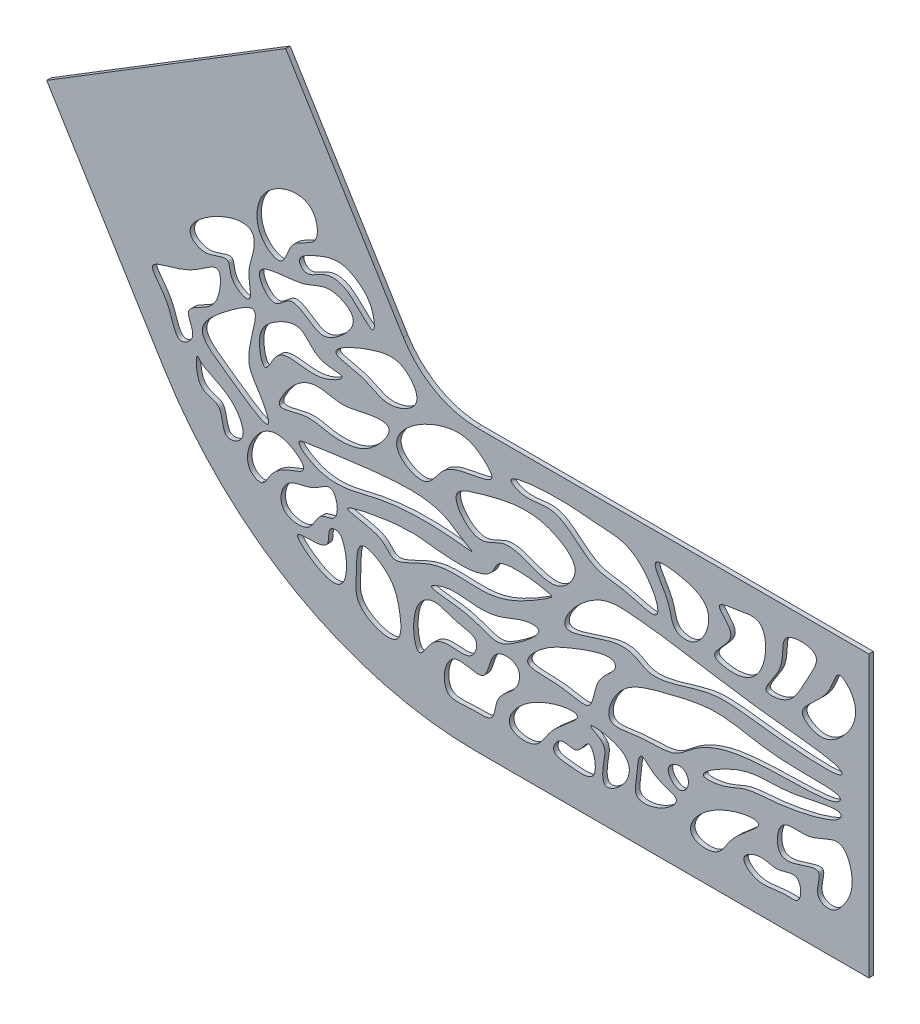
SolidWorks part; units mm, degrees
ref_plane "Alzado" through (0, 0, 0) normal (0, 0, 1) x (1, 0, 0)
ref_plane "Planta" through (0, 0, 0) normal (0, 1, 0) x (1, 0, 0)
ref_plane "Vista lateral" through (0, 0, 0) normal (1, 0, 0) x (0, 0, -1)
sketch "Croquis1" plane through (0, 0, 0) normal (0, 0, 1) x (1, 0, 0)
  line L0 (-108.8464, -21.6986) -> (-38.8648, -21.6986)
  line L1 (-108.7179, 28.3014) -> (-38.8648, 28.3014)
  line L2 (-164.4187, 9.5015) -> (-180.1367, 35.0543)
  line L3 (-121.8307, 35.6981) -> (-137.5487, 61.2509)
  line L8 (-38.8648, 28.3014) -> (-38.8648, -21.6986)
  line L9 (-185.376, 43.5719) -> (-142.7881, 69.7685)
  line L10 (-137.5487, 61.2509) -> (-142.7881, 69.7685)
  line L11 (-180.1367, 35.0543) -> (-185.376, 43.5719)
  arc A0 (-164.4187, 9.5015) -> (-108.8464, -21.6986) centre (-108.5959, 43.8391) ccw
  arc A1 (-121.8307, 35.6981) -> (-108.7179, 28.3014) centre (-108.5959, 43.8391) ccw
  spline S0 degree 3 poles (-100.4055, 3.1812) (-96.2096, 2.6407) (-101.6833, -1.5799) (-105.0602, -3.3903) (-109.3149, -1.5246) (-112.0327, -1.0245) (-118.0527, -0.4678) (-113.717, 1.2519) (-110.3815, 0.7431) (-104.7095, 0.4434) (-100.4055, 3.1812) (-96.2096, 2.6407) (-101.6833, -1.5799) knots -0.315598 -0.18303 -0.018303 0 0.157145 0.229142 0.313252 0.454214 0.526143 0.577742 0.684402 0.81697 0.981697 1 1.157145 1.229142 1.313252 only from (-97.9879, 2.8318) to (-97.9879, 2.8318)
  spline S1 degree 3 poles (-95.9708, 8.2792) (-94.8978, 9.2475) (-104.9487, 10.9619) (-106.2863, 4.0053) (-119.0084, 6.6049) (-121.4988, 6.1089) (-121.9242, 6.6756) (-135.6785, 4.0526) (-124.9898, 3.3533) (-123.9896, -0.7488) (-114.1156, 5.6842) (-106.5443, 1.3252) (-95.9708, 8.2792) (-94.8978, 9.2475) (-104.9487, 10.9619) knots -0.283645 -0.122304 -0.01223 0 0.069569 0.096182 0.247246 0.281231 0.417147 0.513763 0.586005 0.643687 0.716355 0.877696 0.98777 1 1.069569 1.096182 1.247246 only from (-95.3982, 8.9779) to (-95.3982, 8.9779)
  spline S2 degree 3 poles (-107.3413, 7.7106) (-113.3834, 10.7699) (-114.9259, 14.2602) (-133.5623, 11.5959) (-141.7052, 10.4053) (-135.231, 5.8797) (-119.8086, 11.3799) (-107.3413, 7.7106) (-113.3834, 10.7699) (-114.9259, 14.2602) knots -0.400334 -0.311414 -0.031141 0 0.352571 0.531394 0.556104 0.599666 0.688586 0.968859 1 1.352571 1.531394 1.556104 only from (-110.4424, 9.293) to (-110.4424, 9.293)
  spline S3 degree 3 poles (-84.2507, 5.5512) (-83.8734, 2.8356) (-88.0597, 0.6541) (-87.7211, -4.9686) (-90.9541, -4.7807) (-94.5619, -3.8245) (-101.6758, -4.5392) (-97.1613, 0.3592) (-92.3688, 2.6509) (-84.2507, 5.5512) (-83.8734, 2.8356) (-88.0597, 0.6541) knots -0.316899 -0.167029 -0.016703 0 0.100038 0.223753 0.272835 0.361932 0.526926 0.683101 0.832971 0.983297 1 1.100038 1.223753 1.272835 only from (-84.0361, 3.6856) to (-84.0361, 3.6856)
  spline S4 degree 3 poles (-43.868, -0.7672) (-43.7102, 2.1599) (-55.24, -1.3998) (-60.0633, 0.7583) (-70.5442, -5.7193) (-64.4294, -5.2693) (-60.8295, -3.0718) (-54.31, -3.2065) (-43.868, -0.7672) (-43.7102, 2.1599) (-55.24, -1.3998) knots -0.352515 -0.233319 -0.023332 0 0.173914 0.388453 0.503873 0.557099 0.647485 0.766681 0.976668 1 1.173914 1.388453 1.503873 only from (-43.8469, 1.0338) to (-43.8469, 1.0338)
  spline S5 degree 3 poles (-45.1762, 1.1703) (-43.1361, 4.4758) (-56.6574, 3.4944) (-65.1405, 6.7295) (-75.3032, 4.0837) (-83.5561, 1.9737) (-86.6828, -6.3448) (-78.8751, -4.5062) (-73.6633, -5.2307) (-69.3516, -0.9035) (-60.2894, 2.5904) (-45.1762, 1.1703) (-43.1361, 4.4758) (-56.6574, 3.4944) knots -0.295039 -0.191816 -0.019182 0 0.11455 0.24602 0.351314 0.440261 0.51992 0.570513 0.65581 0.704961 0.808184 0.980818 1 1.11455 1.24602 1.351314 only from (-43.9298, 3.407) to (-43.9298, 3.407)
  spline S6 degree 3 poles (-42.4061, 6.1723) (-44.7626, 8.8048) (-61.1588, 9.8682) (-75.7985, 13.0975) (-88.9426, 13.5997) (-97.4981, 1.9663) (-81.6724, 9.2245) (-78.2315, 3.8358) (-67.2533, 9.1986) (-59.1086, 7.4821) (-42.4061, 6.1723) (-44.7626, 8.8048) (-61.1588, 9.8682) knots -0.2879 -0.155387 -0.015539 0 0.099677 0.267068 0.297768 0.406678 0.472741 0.561818 0.7121 0.844613 0.984461 1 1.099677 1.267068 1.297768 only from (-44.0875, 7.9226) to (-44.0875, 7.9226)
  spline S7 degree 3 poles (-55.7688, -13.77) (-55.1878, -4.2136) (-49.0734, -6.2918) (-43.5652, -1.4931) (-41.1669, -8.4852) (-42.8129, -12.2637) (-45.3318, -15.0294) (-48.9687, -13.8335) (-45.7299, -6.9917) (-55.7688, -13.77) (-55.1878, -4.2136) (-49.0734, -6.2918) knots -0.371419 -0.276319 -0.113656 0 0.115773 0.264232 0.386481 0.50234 0.57949 0.628581 0.723681 0.886344 1 1.115773 1.264232 1.386481 only from (-54.3633, -5.9471) to (-54.3633, -5.9471)
  spline S8 degree 3 poles (-89.9303, 15.357) (-95.1992, 8.0201) (-102.3681, 15.1916) (-108.6497, 9.5021) (-114.501, 16.4978) (-104.308, 19.5679) (-97.2634, 21.2185) (-89.9303, 15.357) (-95.1992, 8.0201) (-102.3681, 15.1916) knots -0.482978 -0.177957 -0.098974 0 0.209597 0.303826 0.431796 0.517022 0.822043 0.901026 1 1.209597 1.303826 1.431796 only from (-93.8287, 11.2805) to (-93.8287, 11.2805)
  spline S9 degree 3 poles (-92.8384, 25.0424) (-104.6179, 23.9678) (-99.7607, 21.3466) (-94.0994, 23.914) (-88.8244, 16.449) (-82.5807, 16.8034) (-74.1656, 13.4308) (-79.6794, 24.1391) (-87.746, 23.9509) (-92.8384, 25.0424) (-104.6179, 23.9678) (-99.7607, 21.3466) knots -0.391213 -0.273847 -0.12925 0 0.018174 0.122894 0.279654 0.384629 0.472626 0.608787 0.726153 0.87075 1 1.018174 1.122894 1.279654 only from (-102.3447, 22.7981) to (-102.3447, 22.7981)
  spline S10 degree 3 poles (-71.4074, 23.6007) (-79.1145, 24.4495) (-74.0473, 18.8668) (-74.0962, 14.6634) (-69.0518, 13.4732) (-65.6689, 21.0574) (-71.4074, 23.6007) (-79.1145, 24.4495) (-74.0473, 18.8668) knots -0.597987 -0.351672 -0.165698 0 0.195722 0.325152 0.402013 0.648328 0.834302 1 1.195722 1.325152 1.402013 only from (-76.838, 23.4212) to (-76.838, 23.4212)
  spline S11 degree 3 poles (-61.8839, 23.3906) (-67.2302, 22.7481) (-60.7833, 18.6226) (-68.6479, 14.2898) (-61.93, 12.7387) (-56.9891, 15.3549) (-56.8321, 24.5733) (-61.8839, 23.3906) (-67.2302, 22.7481) (-60.7833, 18.6226) knots -0.438785 -0.218352 -0.095301 0 0.113934 0.288077 0.377524 0.561215 0.781648 0.904699 1 1.113934 1.288077 1.377524 only from (-65.5021, 22.4009) to (-65.5021, 22.4009)
  spline S12 degree 3 poles (-46.5328, 24.3689) (-55.4956, 24.5197) (-52.9941, 18.3631) (-58.8247, 13.0598) (-52.3517, 13.3454) (-50.8304, 17.697) (-46.5328, 24.3689) (-55.4956, 24.5197) (-52.9941, 18.3631) knots -0.577089 -0.309658 -0.16535 0 0.184162 0.363281 0.422911 0.690342 0.83465 1 1.184162 1.363281 1.422911 only from (-53.3642, 23.579) to (-53.3642, 23.579)
  spline S13 degree 3 poles (-47.3156, 10.5592) (-53.1941, 13.8063) (-45.7071, 16.9785) (-44.6822, 23.6828) (-39.6806, 18.815) (-42.7244, 13.2199) (-47.3156, 10.5592) (-53.1941, 13.8063) (-45.7071, 16.9785) knots -0.509276 -0.239068 -0.105487 0 0.2678 0.390798 0.490724 0.760932 0.894513 1 1.2678 1.390798 1.490724 only from (-50.5162, 12.7661) to (-50.5162, 12.7661)
  spline S14 degree 3 poles (-114.3123, 27.5218) (-127.7642, 19.0347) (-116.9289, 13.759) (-114.9315, 21.4169) (-103.8286, 20.3023) (-108.4139, 25.0459) (-114.3123, 27.5218) (-127.7642, 19.0347) (-116.9289, 13.759) knots -0.520669 -0.45976 -0.334427 0 0.125653 0.267573 0.479331 0.54024 0.665573 1 1.125653 1.267573 1.479331 only from (-122.6003, 17.4019) to (-122.6003, 17.4019)
  spline S15 degree 3 poles (-124.8384, 22.9479) (-117.5427, 26.4016) (-121.8712, 31.9946) (-127.1678, 31.4577) (-137.2402, 26.9685) (-128.4706, 26.2208) (-124.8384, 22.9479) (-117.5427, 26.4016) (-121.8712, 31.9946) knots -0.472759 -0.332235 -0.177614 0 0.136647 0.282006 0.527241 0.667765 0.822386 1 1.136647 1.282006 1.527241 only from (-119.4126, 27.1855) to (-119.4126, 27.1855)
  spline S16 degree 3 poles (-129.234, 20.564) (-122.3531, 21.6843) (-126.9414, 15.708) (-130.5959, 14.1258) (-135.2719, 14.0042) (-138.8407, 15.5363) (-145.1218, 12.9324) (-141.8386, 18.6302) (-138.0302, 21.2681) (-132.91, 19.5279) (-129.234, 20.564) (-122.3531, 21.6843) (-126.9414, 15.708) knots -0.286611 -0.187119 -0.108143 0 0.112894 0.20603 0.295443 0.40419 0.500293 0.567623 0.713389 0.812881 0.891857 1 1.112894 1.20603 1.295443 only from (-124.4482, 20.4625) to (-124.4482, 20.4625)
  spline S17 degree 3 poles (-137.6702, 24.1356) (-130.8633, 24.7204) (-138.5446, 20.2847) (-143.6646, 24.5688) (-146.6063, 17.0402) (-148.2178, 23.6202) (-145.2568, 26.6521) (-139.5982, 29.0688) (-137.6702, 24.1356) (-130.8633, 24.7204) (-138.5446, 20.2847) knots -0.352083 -0.229209 -0.097257 0 0.098282 0.334563 0.412197 0.510953 0.647917 0.770791 0.902743 1 1.098282 1.334563 1.412197 only from (-132.7506, 24.1353) to (-132.7506, 24.1353)
  spline S18 degree 3 poles (-132.9555, 30.0213) (-137.3951, 27.7667) (-141.3938, 33.2812) (-144.8297, 28.0526) (-150.2386, 35.0566) (-139.6852, 33.9035) (-135.4498, 37.4594) (-128.8707, 34.3929) (-132.9555, 30.0213) (-137.3951, 27.7667) (-141.3938, 33.2812) knots -0.322381 -0.205976 -0.070065 0 0.160698 0.23687 0.338533 0.549422 0.677619 0.794024 0.929935 1 1.160698 1.23687 1.338533 only from (-136.3173, 28.837) to (-136.3173, 28.837)
  spline S19 degree 3 poles (-127.2551, 37.7466) (-126.517, 31.9582) (-131.4569, 38.7164) (-135.8465, 38.9472) (-139.0186, 36.3001) (-141.0989, 38.7954) (-136.523, 41.0093) (-133.0068, 42.0964) (-129.2255, 39.9202) (-127.2551, 37.7466) (-126.517, 31.9582) (-131.4569, 38.7164) knots -0.283469 -0.193959 -0.083465 0 0.17174 0.311461 0.414653 0.444427 0.554647 0.716531 0.806041 0.916535 1 1.17174 1.311461 1.414653 only from (-127.0917, 34.2547) to (-127.0917, 34.2547)
  spline S20 degree 3 poles (-153.9745, 23.6251) (-145.9826, 29.1645) (-150.7946, 18.5836) (-147.5723, 14.7564) (-144.0136, 7.6492) (-153.0248, 14.321) (-159.7256, 18.7033) (-153.9745, 23.6251) (-145.9826, 29.1645) (-150.7946, 18.5836) knots -0.426096 -0.279271 -0.118317 0 0.192488 0.293022 0.387178 0.573904 0.720729 0.881683 1 1.192488 1.293022 1.387178 only from (-148.529, 26.6062) to (-148.529, 26.6062)
  spline S21 degree 3 poles (-55.2274, -13.7251) (-50.8574, -11.1441) (-50.705, -16.5564) (-55.1905, -15.9395) (-58.4243, -17.6543) (-62.1609, -14.0138) (-57.9612, -12.0342) (-55.2274, -13.7251) (-50.8574, -11.1441) (-50.705, -16.5564) knots -0.419869 -0.272796 -0.144259 0 0.160267 0.210766 0.504987 0.580131 0.727204 0.855741 1 1.160267 1.210766 1.504987 only from (-51.6792, -12.6886) to (-51.6792, -12.6886)
  spline S22 degree 3 poles (-67.6542, -8.2805) (-72.4924, -16.003) (-65.6748, -16.6786) (-63.614, -12.4117) (-61.017, -10.3992) (-56.3303, -6.3587) (-67.6542, -8.2805) (-72.4924, -16.003) (-65.6748, -16.6786) knots -0.566614 -0.504093 -0.218818 0 0.131217 0.261968 0.433386 0.495907 0.781182 1 1.131217 1.261968 1.433386 only from (-70.1781, -15.5973) to (-70.1781, -15.5973)
  spline S23 degree 3 poles (-99.9275, -7.7956) (-104.7656, -15.5181) (-97.948, -16.1937) (-95.8873, -11.9268) (-93.2903, -9.9144) (-88.6036, -5.8738) (-99.9275, -7.7956) (-104.7656, -15.5181) (-97.948, -16.1937) knots -0.566614 -0.504093 -0.218818 0 0.131217 0.261968 0.433386 0.495907 0.781182 1 1.131217 1.261968 1.433386 only from (-102.4513, -15.1124) to (-102.4513, -15.1124)
  spline S24 degree 3 poles (-90.7044, -13.7114) (-93.8141, -11.5745) (-95.8994, -15.2616) (-91.4989, -15.6406) (-86.509, -16.3126) (-88.4979, -8.5136) (-90.7044, -13.7114) (-93.8141, -11.5745) (-95.8994, -15.2616) knots -0.50021 -0.292274 -0.145876 0 0.117021 0.265473 0.49979 0.707726 0.854124 1 1.117021 1.265473 1.49979 only from (-93.8287, -12.572) to (-93.8287, -12.572)
  spline S25 degree 3 poles (-80.1594, -7.8225) (-90.9119, -6.8547) (-85.3096, -9.1276) (-86.3096, -12.1094) (-86.4236, -16.5083) (-81.8895, -13.8633) (-80.1594, -7.8225) (-90.9119, -6.8547) (-85.3096, -9.1276) knots -0.618588 -0.487424 -0.262237 0 0.100832 0.255151 0.381412 0.512576 0.737763 1 1.100832 1.255151 1.381412 only from (-88.3491, -7.7329) to (-88.3491, -7.7329)
  spline S26 degree 3 poles (-76.8185, -10.324) (-79.9765, -6.2217) (-80.118, -11.2204) (-80.9688, -15.0683) (-76.0501, -14.727) (-71.4055, -10.7123) (-76.8185, -10.324) (-79.9765, -6.2217) (-80.118, -11.2204) knots -0.521013 -0.326779 -0.141819 0 0.174988 0.298356 0.478987 0.673221 0.858181 1 1.174988 1.298356 1.478987 only from (-79.3886, -7.7329) to (-79.3886, -7.7329)
  spline S27 degree 3 poles (-71.9311, -5.131) (-75.9801, -6.9854) (-72.5698, -10.6148) (-70.519, -7.8251) (-71.9311, -5.131) (-75.9801, -6.9854) (-72.5698, -10.6148) knots -0.695992 -0.473766 -0.274772 0 0.304008 0.526234 0.725228 1 1.304008 1.526234 1.725228 only from (-74.5935, -7.1958) to (-74.5935, -7.1958)
  spline S28 degree 3 poles (-106.285, -11.5733) (-106.7296, -3.8104) (-100.7975, -4.3413) (-101.2848, -9.2207) (-105.5464, -10.5774) (-105.4198, -15.987) (-109.9024, -15.2962) (-115.4243, -16.6274) (-114.069, -7.0875) (-106.285, -11.5733) (-106.7296, -3.8104) (-100.7975, -4.3413) knots -0.414748 -0.267488 -0.136298 0 0.09281 0.157708 0.299308 0.383949 0.472166 0.585252 0.732512 0.863702 1 1.09281 1.157708 1.299308 only from (-105.0472, -4.7669) to (-105.0472, -4.7669)
  spline S29 degree 3 poles (-116.9345, -8.5594) (-113.6599, -7.2332) (-109.5453, -8.6127) (-108.1136, -3.9651) (-112.7948, -3.6815) (-116.3432, -1.4714) (-120.8072, -4.9288) (-119.6091, -14.1111) (-116.9345, -8.5594) (-113.6599, -7.2332) (-109.5453, -8.6127) knots -0.408616 -0.196902 -0.09815 0 0.139916 0.219187 0.321205 0.480174 0.591384 0.803098 0.90185 1 1.139916 1.219187 1.321205 only from (-113.9347, -7.7329) to (-113.9347, -7.7329)
  spline S30 degree 3 poles (-122.4605, -6.214) (-121.5633, -13.7191) (-130.8452, -10.3851) (-130.0541, -5.114) (-130.3042, 1.6926) (-123.8184, -2.145) (-122.4605, -6.214) (-121.5633, -13.7191) (-130.8452, -10.3851) knots -0.475837 -0.304992 -0.16379 0 0.222453 0.374091 0.524163 0.695008 0.83621 1 1.222453 1.374091 1.524163 only from (-122.9798, -11.4655) to (-122.9798, -11.4655)
  spline S31 degree 3 poles (-131.7069, -2.936) (-131.6896, -10.0276) (-137.6584, -7.5507) (-142.7034, -2.8826) (-134.0857, -4.9334) (-135.6088, 0.0238) (-133.1514, 0.0311) (-131.7069, -2.936) (-131.6896, -10.0276) (-137.6584, -7.5507) knots -0.311497 -0.248093 -0.216943 0 0.243329 0.360779 0.579241 0.688503 0.751907 0.783057 1 1.243329 1.360779 1.579241 only from (-132.7506, -7.7329) to (-132.7506, -7.7329)
  spline S32 degree 3 poles (-142.8882, 4.1867) (-144.535, -2.3549) (-138.0095, -3.2082) (-137.1992, 1.2642) (-132.8436, 1.0923) (-134.0498, 7.5814) (-138.2705, 3.4266) (-142.8882, 4.1867) (-144.535, -2.3549) (-138.0095, -3.2082) knots -0.457136 -0.34329 -0.145044 0 0.167631 0.302485 0.389236 0.542864 0.65671 0.854956 1 1.167631 1.302485 1.389236 only from (-143.2643, -1.3326) to (-143.2643, -1.3326)
  spline S33 degree 3 poles (-148.1282, 9.3257) (-151.0578, 1.7635) (-146.7703, 0.2461) (-145.7179, 2.5054) (-144.0449, 4.237) (-141.8667, 5.1964) (-138.308, 6.3528) (-142.7795, 9.9641) (-148.1282, 9.3257) (-151.0578, 1.7635) (-146.7703, 0.2461) knots -0.593653 -0.458057 -0.281382 0 0.055986 0.125037 0.23029 0.322646 0.406347 0.541943 0.718618 1 1.055986 1.125037 1.23029 only from (-148.529, 1.024) to (-148.529, 1.024)
  spline S34 degree 3 poles (-158.8318, 15.0335) (-157.2516, 12.7956) (-152.2932, 12.1284) (-149.1561, 5.5262) (-154.3564, 3.7675) (-153.6251, 10.0131) (-158.8351, 8.6361) (-158.8318, 15.0335) (-157.2516, 12.7956) (-152.2932, 12.1284) knots -0.28822 -0.12709 -0.012709 0 0.265528 0.46936 0.552103 0.71178 0.87291 0.987291 1 1.265528 1.46936 1.552103 only from (-158.2655, 14.2392) to (-158.2655, 14.2392)
  spline S35 degree 3 poles (-163.081, 20.3877) (-162.4809, 13.8898) (-158.3009, 17.2455) (-161.5248, 21.0043) (-156.4878, 22.5782) (-154.4529, 25.3661) (-154.1097, 31.6548) (-160.058, 25.6322) (-169.0534, 25.3791) (-163.081, 20.3877) (-162.4809, 13.8898) (-158.3009, 17.2455) knots -0.439567 -0.253616 -0.130815 0 0.058503 0.146138 0.242132 0.335973 0.426326 0.560433 0.746384 0.869185 1 1.058503 1.146138 1.242132 only from (-161.1514, 15.3614) to (-161.1514, 15.3614)
  spline S36 degree 3 poles (-152.597, 33.1957) (-152.9183, 28.899) (-148.2503, 26.5347) (-149.925, 32.1094) (-148.514, 34.6827) (-148.1075, 40.2844) (-155.9709, 38.2071) (-161.4268, 32.8978) (-156.6902, 30.3134) (-152.597, 33.1957) (-152.9183, 28.899) (-148.2503, 26.5347) knots -0.254814 -0.174445 -0.066097 0 0.09497 0.186427 0.312723 0.374421 0.581872 0.745186 0.825555 0.933903 1 1.09497 1.186427 1.312723 only from (-152.3501, 29.5381) to (-152.3501, 29.5381)
  spline S37 degree 3 poles (-148.6859, 47.176) (-148.3959, 38.1421) (-142.8842, 35.6775) (-142.2892, 41.2831) (-136.5447, 41.6523) (-137.5947, 49.9035) (-148.6859, 47.176) (-148.3959, 38.1421) (-142.8842, 35.6775) knots -0.655316 -0.523978 -0.262981 0 0.063822 0.191703 0.344684 0.476022 0.737019 1 1.063822 1.191703 1.344684 only from (-145.8367, 37.1866) to (-145.8367, 37.1866)
  point P562 (-47.8423, -12.6886)
  dimension "D1" = 30
extrude "Saliente-Extruir1" add sketch "Croquis1" along normal blind 0.8
